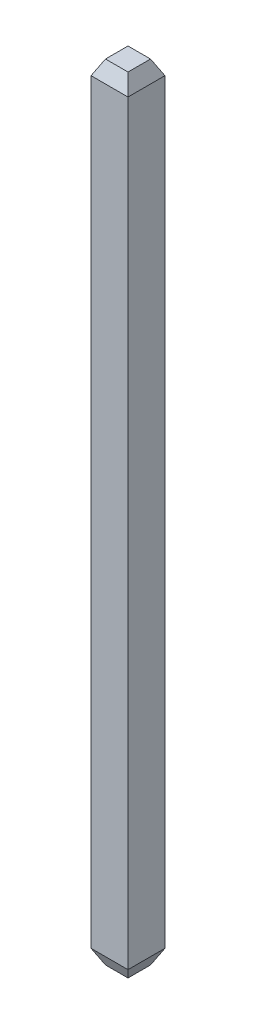
SolidWorks part; units mm, degrees
ref_plane "Front Plane" through (0, 0, 0) normal (0, 0, 1) x (1, 0, 0)
ref_plane "Top Plane" through (0, 0, 0) normal (0, 1, 0) x (1, 0, 0)
ref_plane "Right Plane" through (0, 0, 0) normal (1, 0, 0) x (0, 0, -1)
sketch "Sketch1" plane through (0, 0, 0) normal (0, 1, 0) x (1, 0, 0)
  line L1 (-0.32, 0.32) -> (0.32, 0.32)
  line L2 (-0.32, 0.32) -> (-0.32, -0.32)
  line L3 (-0.32, -0.32) -> (0.32, -0.32)
  line L4 (0.32, 0.32) -> (0.32, -0.32)
  line L5 (-0.32, 0.32) -> (0.32, -0.32) construction
  line L6 (-0.32, -0.32) -> (0.32, 0.32) construction
  point P0 (0, 0)
  dimension "D1" = 0.64
extrude "Extrude1" add sketch "Sketch1" along normal blind 13.59
chamfer "Chamfer1" distance 0.25 distance2 0.125 4 edges at (0, 13.59, -0.32) (-0.32, 13.59, 0) (0, 13.59, 0.32) (0.32, 13.59, 0)
chamfer "Chamfer2" distance 0.125 distance2 0.25 4 edges at (0, 0, -0.32) (-0.32, 0, 0) (0, 0, 0.32) (0.32, 0, 0)
